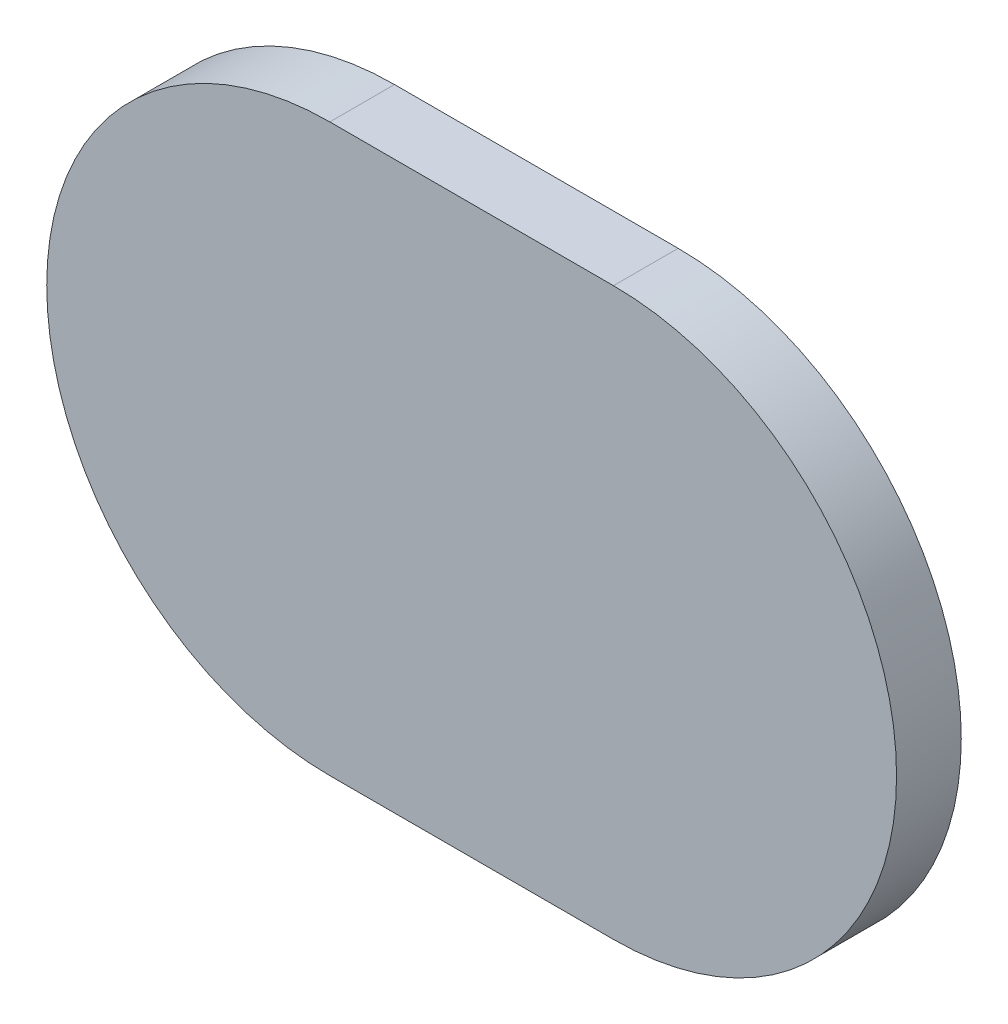
SolidWorks part; units mm, degrees
ref_plane "Front Plane" through (0, 0, 0) normal (0, 0, 1) x (1, 0, 0)
ref_plane "Top Plane" through (0, 0, 0) normal (0, 1, 0) x (1, 0, 0)
ref_plane "Right Plane" through (0, 0, 0) normal (1, 0, 0) x (0, 0, -1)
sketch "Sketch1" plane through (0, 0, 0) normal (0, 0, 1) x (1, 0, 0)
  line L0 (0, 5.5563) -> (-5.5671, 5.5562)
  line L1 (0, -5.5563) -> (-5.5671, -5.5563)
  arc A0 (0, -5.5563) -> (0, 5.5563) centre (0, 0) ccw
  arc A1 (-5.5671, 5.5562) -> (-5.5671, -5.5563) centre (-5.5671, 0) ccw
  dimension "D1" = 11.1125
  dimension "D2" = 5.5563
  dimension "D3" = 5.5671
extrude "Boss-Extrude1" add sketch "Sketch1" along normal blind 1.27
